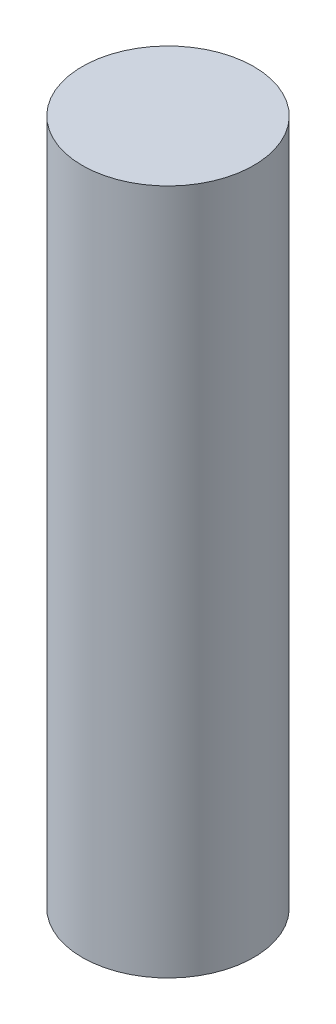
SolidWorks part; units mm, degrees
ref_plane "Front Plane" through (0, 0, 0) normal (0, 0, 1) x (1, 0, 0)
ref_plane "Top Plane" through (0, 0, 0) normal (0, 1, 0) x (1, 0, 0)
ref_plane "Right Plane" through (0, 0, 0) normal (1, 0, 0) x (0, 0, -1)
sketch "Sketch1" plane through (0, 0, 0) normal (0, 1, 0) x (1, 0, 0)
  circle A0 centre (0, 0) radius 38.1
  dimension "D1" = 76.2
extrude "Boss-Extrude1" add sketch "Sketch1" along normal blind 304.8
